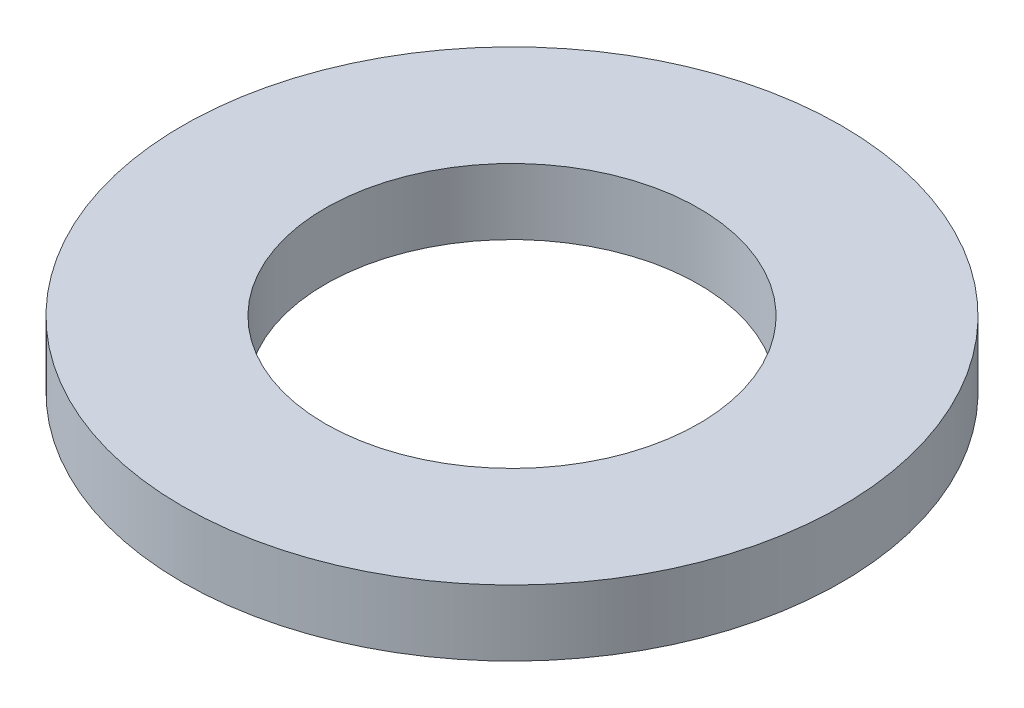
SolidWorks part; units mm, degrees
ref_plane "Front Plane" through (0, 0, 0) normal (0, 0, 1) x (1, 0, 0)
ref_plane "Top Plane" through (0, 0, 0) normal (0, 1, 0) x (1, 0, 0)
ref_plane "Right Plane" through (0, 0, 0) normal (1, 0, 0) x (0, 0, -1)
sketch "Sketch1" plane through (0, 0, 0) normal (0, 0, 1) x (1, 0, 0)
  line L0 (0, 2.9683) -> (0, 0) construction
  line L1 (0, 0) -> (-15, 0) construction
  line L3 (-15, 0) -> (-8.5, 0)
  line L4 (-15, 0) -> (-15, -3)
  line L5 (-15, -3) -> (-8.5, -3)
  line L6 (-8.5, 0) -> (-8.5, -3)
  dimension "D1" = 8.5
  dimension "D2" = 15
  dimension "D3" = 3
revolve "Revolve1" add sketch "Sketch1" angle 360 about L0
